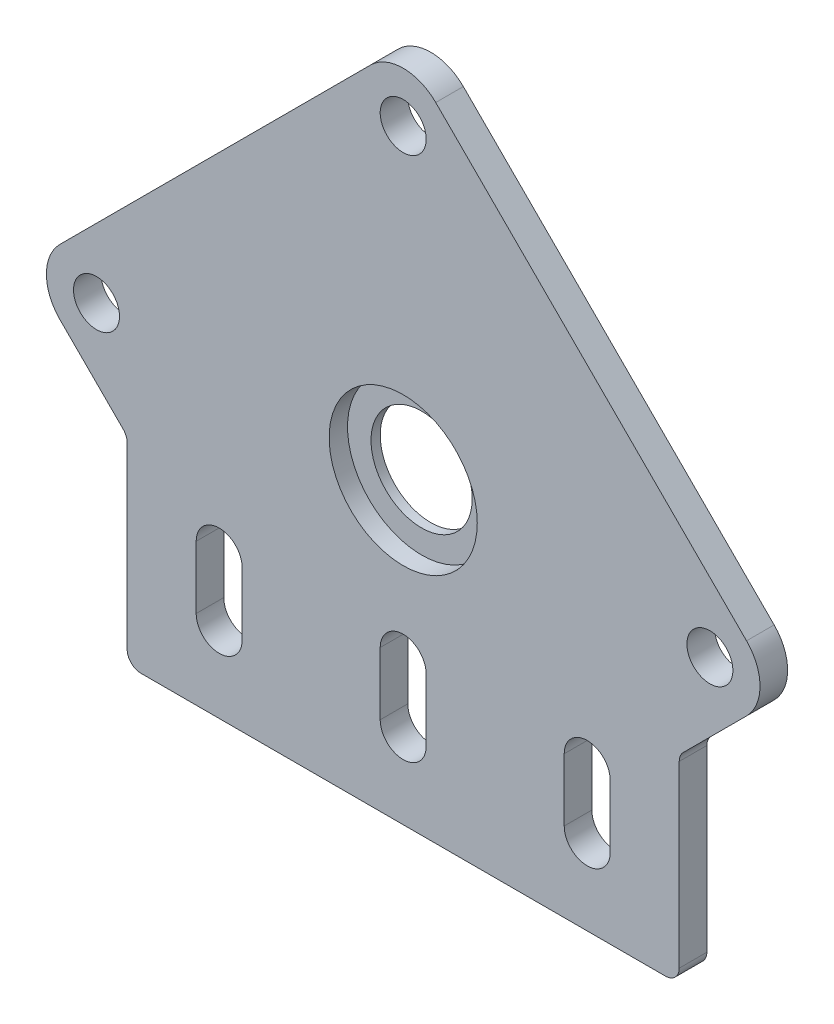
SolidWorks part; units mm, degrees
ref_plane "Front" through (0, 0, 0) normal (0, 0, 1) x (1, 0, 0)
ref_plane "Top" through (0, 0, 0) normal (0, 1, 0) x (1, 0, 0)
ref_plane "Right" through (0, 0, 0) normal (1, 0, 0) x (0, 0, -1)
sketch "Model" plane through (0, 0, 0) normal (0, 0, 1) x (1, 0, 0)
  line L0 (-28.5, 0) -> (28.5, 0)
  line L1 (-37.314, 28.8945) -> (-30.4393, 22.0198)
  line L2 (-30, 20.9591) -> (-30, 1.5)
  line L3 (-3.5355, 69.744) -> (-37.314, 35.9655)
  line L4 (20, 8.63) -> (20, 15.43) construction
  line L5 (22.5, 8.63) -> (22.5, 15.43)
  line L6 (-20, 8.63) -> (-20, 15.43) construction
  line L7 (-22.5, 8.63) -> (-22.5, 15.43)
  line L8 (17.5, 8.63) -> (17.5, 15.43)
  line L10 (30, 20.9591) -> (30, 1.5)
  line L11 (37.314, 28.8945) -> (30.4393, 22.0198)
  line L12 (3.5355, 69.744) -> (37.314, 35.9655)
  line L13 (0, 0) -> (0, 71.2085) construction
  line L14 (-38.7785, 32.43) -> (38.7785, 32.43) construction
  line L15 (0, 8.63) -> (0, 15.43) construction
  line L16 (-2.5, 8.63) -> (-2.5, 15.43)
  line L17 (2.5, 8.63) -> (2.5, 15.43)
  line L18 (-17.5, 8.63) -> (-17.5, 15.43)
  arc A0 (30, 1.5) -> (28.5, 0) centre (28.5, 1.5) cw
  circle A1 centre (0, 32.43) radius 5.5
  arc A2 (30, 20.9591) -> (30.4393, 22.0198) centre (31.5, 20.9591) cw
  arc A3 (3.5355, 69.744) -> (-3.5355, 69.744) centre (0, 66.2085) ccw
  arc A4 (-37.314, 35.9655) -> (-37.314, 28.8945) centre (-33.7785, 32.43) ccw
  circle A5 centre (0, 65.763) radius 2.5
  circle A6 centre (33.333, 32.43) radius 2.5
  circle A7 centre (-33.333, 32.43) radius 2.5
  arc A8 (22.5, 8.63) -> (17.5, 8.63) centre (20, 8.63) cw
  arc A9 (17.5, 15.43) -> (22.5, 15.43) centre (20, 15.43) cw
  arc A10 (-22.5, 8.63) -> (-17.5, 8.63) centre (-20, 8.63) ccw
  arc A11 (-17.5, 15.43) -> (-22.5, 15.43) centre (-20, 15.43) ccw
  arc A14 (37.314, 35.9655) -> (37.314, 28.8945) centre (33.7785, 32.43) cw
  arc A15 (-2.5, 8.63) -> (2.5, 8.63) centre (0, 8.63) ccw
  arc A16 (-30, 20.9591) -> (-30.4393, 22.0198) centre (-31.5, 20.9591) ccw
  arc A17 (-30, 1.5) -> (-28.5, 0) centre (-28.5, 1.5) ccw
  arc A18 (2.5, 15.43) -> (-2.5, 15.43) centre (0, 15.43) ccw
  point P20 (20, 12.03)
  point P26 (-20, 12.03)
  point P54 (0, 12.03)
  dimension "D1" = 11
  dimension "D2" = 5
  dimension "D3" = 1.5
  dimension "D4" = 5
  dimension "D5" = 60
  dimension "D12" = 2.5
  dimension "D14" = 6.13
  dimension "D6" = 71.2085
  dimension "D7" = 45
  dimension "D8" = 47.77
  dimension "D9" = 135
  dimension "D10" = 33.333
  dimension "D11" = 33.333
  dimension "D13" = 6.8
  dimension "D15" = 20
extrude "Boss-Extrude1" add sketch "Model" along normal blind 3
sketch "Sketch2" plane through (0, 0, 3) normal (0, 0, 1) x (1, 0, 0)
  circle A0 centre (0, 32.43) radius 8.05
  dimension "D1" = 16.1
extrude "Cut-Extrude1" cut sketch "Sketch2" against normal blind 2
